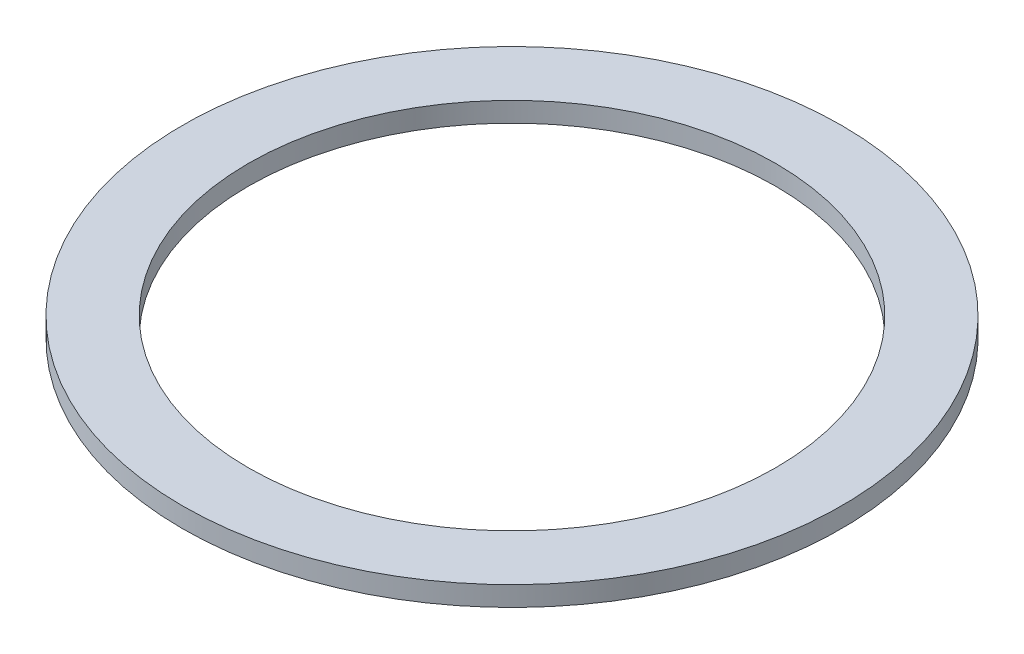
SolidWorks part; units mm, degrees
ref_plane "Front Plane" through (0, 0, 0) normal (0, 0, 1) x (1, 0, 0)
ref_plane "Top Plane" through (0, 0, 0) normal (0, 1, 0) x (1, 0, 0)
ref_plane "Right Plane" through (0, 0, 0) normal (1, 0, 0) x (0, 0, -1)
sketch "Sketch1" plane through (0, 0, 0) normal (0, 1, 0) x (1, 0, 0)
  circle A0 centre (0, 0) radius 500
  circle A1 centre (0, 0) radius 400
  dimension "D1" = 1000
  dimension "D2" = 100
extrude "Boss-Extrude1" add sketch "Sketch1" along normal blind 30
